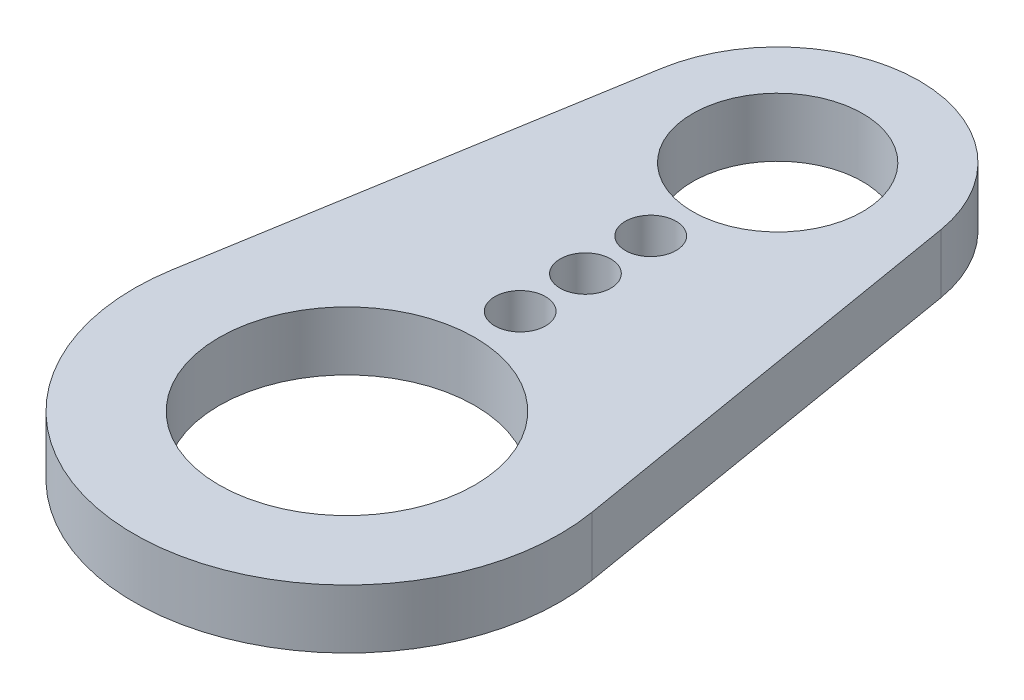
SolidWorks part; units mm, degrees
material "6061 Alloy"
ref_plane "Front Plane" through (0, 0, 0) normal (0, 0, 1) x (1, 0, 0)
ref_plane "Top Plane" through (0, 0, 0) normal (0, 1, 0) x (1, 0, 0)
ref_plane "Right Plane" through (0, 0, 0) normal (1, 0, 0) x (0, 0, -1)
sketch "Sketch1" plane through (0, 0, 0) normal (0, 1, 0) x (1, 0, 0)
  line L0 (3.9142, 12.7209) -> (5.8807, 0.9854)
  line L1 (-3.9142, 12.7209) -> (-5.8807, 0.9854)
  circle A0 centre (0, 0) radius 3.5814
  circle A1 centre (0, 4.8514) radius 0.7112
  circle A2 centre (0, 6.6802) radius 0.7112
  circle A3 centre (0, 8.509) radius 0.7112
  circle A4 centre (0, 12.065) radius 2.3813
  arc A5 (-5.8807, 0.9854) -> (5.8807, 0.9854) centre (0, 0) ccw
  arc A6 (-3.9142, 12.7209) -> (3.9142, 12.7209) centre (0, 12.065) cw
  dimension "D1" = 7.1628
  dimension "D2" = 1.4224
  dimension "D4" = 4.7625
  dimension "D6" = 2.3813
  dimension "D7" = 1.5875
  dimension "D3" = 4.8514
  dimension "D5" = 12.065
extrude "Extrude1" add sketch "Sketch1" along normal mid plane 1.651
